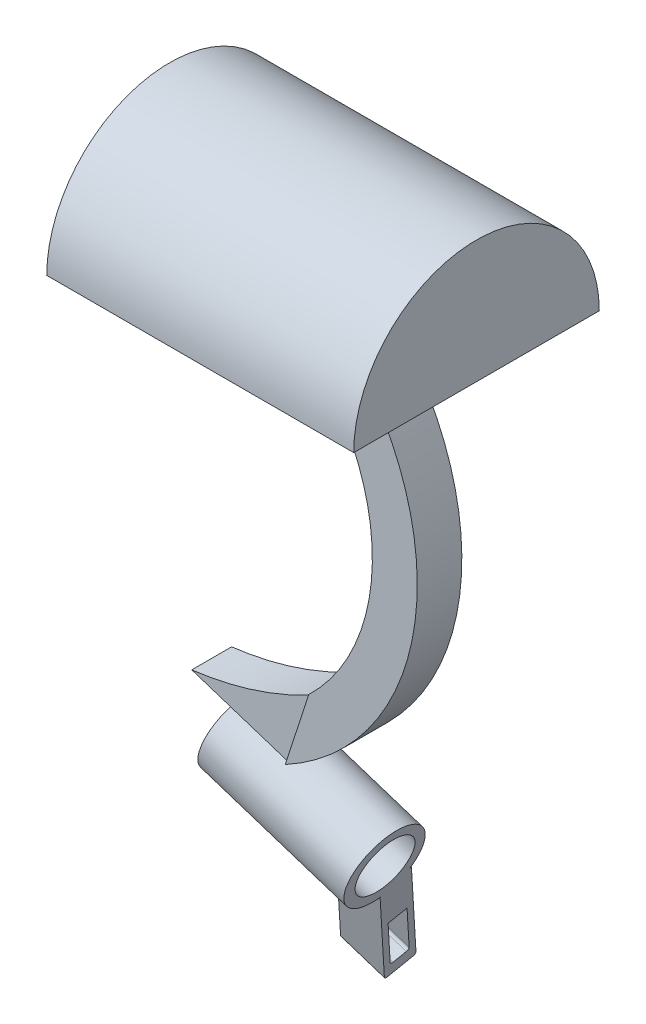
SolidWorks part; units mm, degrees
ref_plane "Front Plane" through (0, 0, 0) normal (0, 0, 1) x (1, 0, 0)
ref_plane "Top Plane" through (0, 0, 0) normal (0, 1, 0) x (1, 0, 0)
ref_plane "Right Plane" through (0, 0, 0) normal (1, 0, 0) x (0, 0, -1)
sketch "Sketch1" plane through (0, 0, 0) normal (0, 1, 0) x (1, 0, 0)
  line L1 (0, 0.371) -> (25.4, 0.371)
  line L2 (0, 0.371) -> (0, 10.531)
  line L3 (0, 10.531) -> (25.4, 10.531)
  line L4 (25.4, 0.371) -> (25.4, 10.531)
  dimension "D1" = 25.4
  dimension "D2" = 10.16
revolve "Revolve1" add sketch "Sketch1" angle 180 about L1
sketch "Sketch4" plane through (0, 0, 0) normal (0, 1, 0) x (1, 0, 0)
  line L0 (12.7, -9.789) -> (12.7, 10.531) construction
  line L1 (25.4, -9.789) -> (0, -9.789) construction
  line L2 (25.4, 10.531) -> (0, 10.531) construction
  line L3 (0, 0.371) -> (25.4, 0.371) construction
  line L4 (0, -9.789) -> (0, 10.531) construction
  line L5 (25.4, 10.531) -> (25.4, -9.789) construction
  line L7 (9.555, 2.216) -> (15.845, 2.216)
  line L8 (9.555, 2.216) -> (9.555, -1.474)
  line L9 (9.555, -1.474) -> (15.845, -1.474)
  line L10 (15.845, 2.216) -> (15.845, -1.474)
  line L11 (9.555, 2.216) -> (15.845, -1.474) construction
  line L12 (9.555, -1.474) -> (15.845, 2.216) construction
  point P12 (12.7, 0.371)
  dimension "D1" = 6.29
  dimension "D2" = 3.69
sketch "Sketch5" plane through (0, 0, 0) normal (0, 0, 1) x (1, 0, 0)
  line L0 (12.7, 0) -> (12.7, -28.9) construction
  line L1 (9.555, 0) -> (15.845, 0) construction
  arc A0 (12.7, 0) -> (12.3926, -30.5071) centre (1.4568, -15.1418) cw
  dimension "D1" = 28.9
sweep "Sweep1" add profiles "Sketch4" path "Sketch5"
ref_plane "Plane2" through (20.1643, -6.5381, 0) normal (-0.9512, 0.3084, 0) x (0, 0, 1)
sketch "Sketch6" plane through (20.1643, -6.5381, 0) normal (-0.9512, 0.3084, 0) x (0, 0, 1)
  line L1 (1.2864, -22.2174) -> (-2.0086, -22.2174)
  line L2 (1.2864, -22.2174) -> (1.2864, -28.1924)
  line L3 (1.2864, -28.1924) -> (-2.0086, -28.1924)
  line L4 (-2.0086, -22.2174) -> (-2.0086, -28.1924)
  line L5 (1.2864, -22.2174) -> (-2.0086, -28.1924) construction
  line L6 (1.2864, -28.1924) -> (-2.0086, -22.2174) construction
  point P0 (-0.3611, -25.2049)
extrude "Boss-Extrude1" add sketch "Sketch6" along normal blind 5.08
ref_plane "Plane3" through (15.332, -4.9713, 0) normal (-0.9512, 0.3084, 0) x (0, 0, 1)
sketch "Sketch7" plane through (15.332, -4.9713, 0) normal (-0.9512, 0.3084, 0) x (0, 0, 1)
  line L0 (-0.3611, -22.2174) -> (-0.3611, -30.7339) construction
  line L1 (1.2864, -22.2174) -> (-2.0086, -22.2174) construction
  line L2 (-2.0086, -28.1924) -> (1.2864, -28.1924) construction
  circle A0 centre (-0.3611, -31.161) radius 3.22
  point P8 (-0.3611, -28.1924)
  dimension "D1" = 2.9686
extrude "Boss-Extrude7" add sketch "Sketch7" against normal blind 12.7
sketch "Sketch9" plane through (15.332, -4.9713, 0) normal (-0.9512, 0.3084, 0) x (0, 0, 1)
  line L1 (1.2864, -28.1924) -> (-2.0086, -28.1924)
  line L2 (1.2864, -28.1924) -> (1.2864, -22.2174)
  line L3 (1.2864, -22.2174) -> (-2.0086, -22.2174)
  line L4 (-2.0086, -28.1924) -> (-2.0086, -22.2174)
extrude "Boss-Extrude8" add sketch "Sketch9" along normal blind 3.302
sketch "Sketch10" plane through (0, 0, 0) normal (0, 0, 1) x (1, 0, 0)
  line L0 (3.4955, -30.7707) -> (5.3384, -25.0871)
  line L1 (5.3384, -25.0871) -> (13.3117, -27.6723)
  spline S0 degree 2 poles (13.3117, -27.6723) (8.6837, -30.1294) (3.4955, -30.7707) knots 0 0 0 1 1 1
extrude "Cut-Extrude1" cut sketch "Sketch10" against normal blind 3.302 and the other way blind 3.302
ref_plane "Plane6" through (27.4128, -8.8884, 0) normal (0.9512, -0.3084, 0) x (0, 0, -1)
sketch "Sketch11" plane through (27.4128, -8.8884, 0) normal (0.9512, -0.3084, 0) x (0, 0, -1)
  line L0 (0.4223, -27.8725) -> (0.3611, -34.381) construction
  line L1 (-2.8589, -31.161) -> (3.5811, -31.161) construction
  circle A0 centre (0.3611, -31.161) radius 3.22 construction
  circle A1 centre (0.3917, -31.1268) radius 2.375
  dimension "D1" = 4.75
extrude "Cut-Extrude2" cut sketch "Sketch11" against normal blind 12.446 and the other way blind 2.54
sketch "Sketch13" plane through (27.4128, -8.8884, 0) normal (0.9512, -0.3084, 0) x (0, 0, -1)
  line L15 (6.5199, -42.695) -> (3.1253, -32.9109)
  line L16 (4.4489, -43.6555) -> (6.3788, -42.9859)
  line L17 (0.9727, -34.3336) -> (4.158, -43.5144)
  line L18 (3.1253, -32.9109) -> (0.9727, -34.3336)
  line L19 (4.0988, -37.2424) -> (5.6628, -41.7502)
  line L20 (2.6817, -37.7341) -> (4.0988, -37.2424)
  line L21 (4.2457, -42.2419) -> (2.6817, -37.7341)
  line L22 (5.5218, -42.0411) -> (4.5366, -42.3829)
  arc A6 (6.3788, -42.9859) -> (6.5199, -42.695) centre (6.3039, -42.7699) ccw
  arc A7 (4.158, -43.5144) -> (4.4489, -43.6555) centre (4.3739, -43.4395) ccw
  arc A8 (4.2457, -42.2419) -> (4.5366, -42.3829) centre (4.4617, -42.1669) ccw
  arc A9 (5.6628, -41.7502) -> (5.5218, -42.0411) centre (5.4469, -41.8251) cw
extrude "Boss-Extrude14" add sketch "Sketch13" against normal blind 3.81
sketch "Sketch15" plane through (27.4128, -8.8884, 0) normal (0.9512, -0.3084, 0) x (0, 0, -1)
  circle A0 centre (0.3917, -31.1268) radius 2.375
extrude "Cut-Extrude3" cut sketch "Sketch15" against normal blind 22.352
